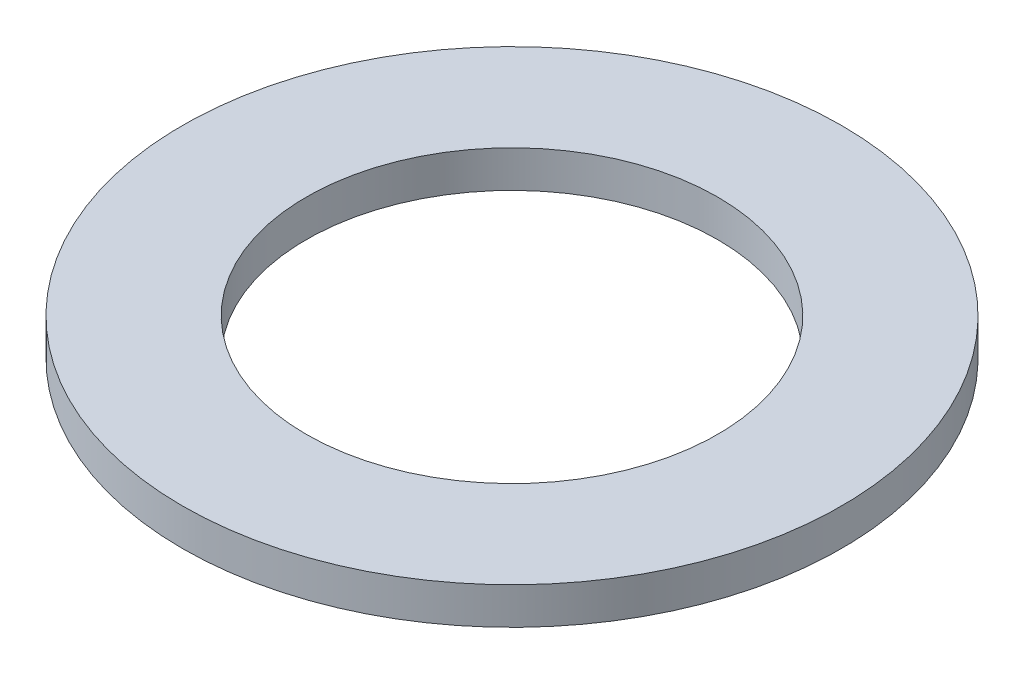
SolidWorks part; units mm, degrees
ref_plane "Front Plane" through (0, 0, 0) normal (0, 0, 1) x (1, 0, 0)
ref_plane "Top Plane" through (0, 0, 0) normal (0, 1, 0) x (1, 0, 0)
ref_plane "Right Plane" through (0, 0, 0) normal (1, 0, 0) x (0, 0, -1)
sketch "Sketch1" plane through (0, 0, 0) normal (0, 1, 0) x (1, 0, 0)
  circle A0 centre (0, 0) radius 7.9375
  dimension "OD" = 15.875
extrude "Boss-Extrude1" add sketch "Sketch1" along normal blind 0.889
sketch "Sketch5" plane through (0, 0.889, 0) normal (0, 1, 0) x (-1, 0, 0)
  circle A0 centre (0, 0) radius 4.953
  dimension "ID" = 9.906
extrude "Cut-Extrude1" cut sketch "Sketch5" against normal through all
